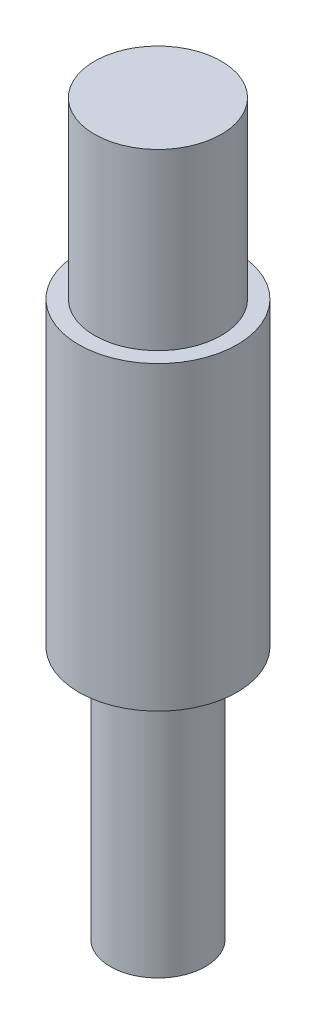
SolidWorks part; units mm, degrees
material "非常高密度 PE (SS)"
ref_plane "前视基准面" through (0, 0, 0) normal (0, 0, 1) x (1, 0, 0)
ref_plane "上视基准面" through (0, 0, 0) normal (0, 1, 0) x (1, 0, 0)
ref_plane "右视基准面" through (0, 0, 0) normal (1, 0, 0) x (0, 0, -1)
sketch "草图1" plane through (0, 0, 0) normal (0, 0, 1) x (1, 0, 0)
  line L0 (0, 9.186) -> (0, -28.4029) construction
  line L1 (0, 0) -> (2, 0)
  line L2 (2.5, -5.5) -> (2.5, -15)
  line L3 (2.5, -15) -> (1.5, -15)
  line L4 (1.5, -15) -> (1.5, -23)
  line L5 (1.5, -23) -> (0, -23)
  line L6 (0, -23) -> (0, 0)
  line L7 (2, 0) -> (2, -5.5)
  line L8 (2, -5.5) -> (2.5, -5.5)
  dimension "D1" = 15
  dimension "D2" = 5.5
  dimension "D3" = 1.5
  dimension "D4" = 23
  dimension "D5" = 2
  dimension "D6" = 2.5
revolve "旋转1" add sketch "草图1" angle 360 about L0
cosmetic thread "装饰螺纹线1" parameters "D2"=2
